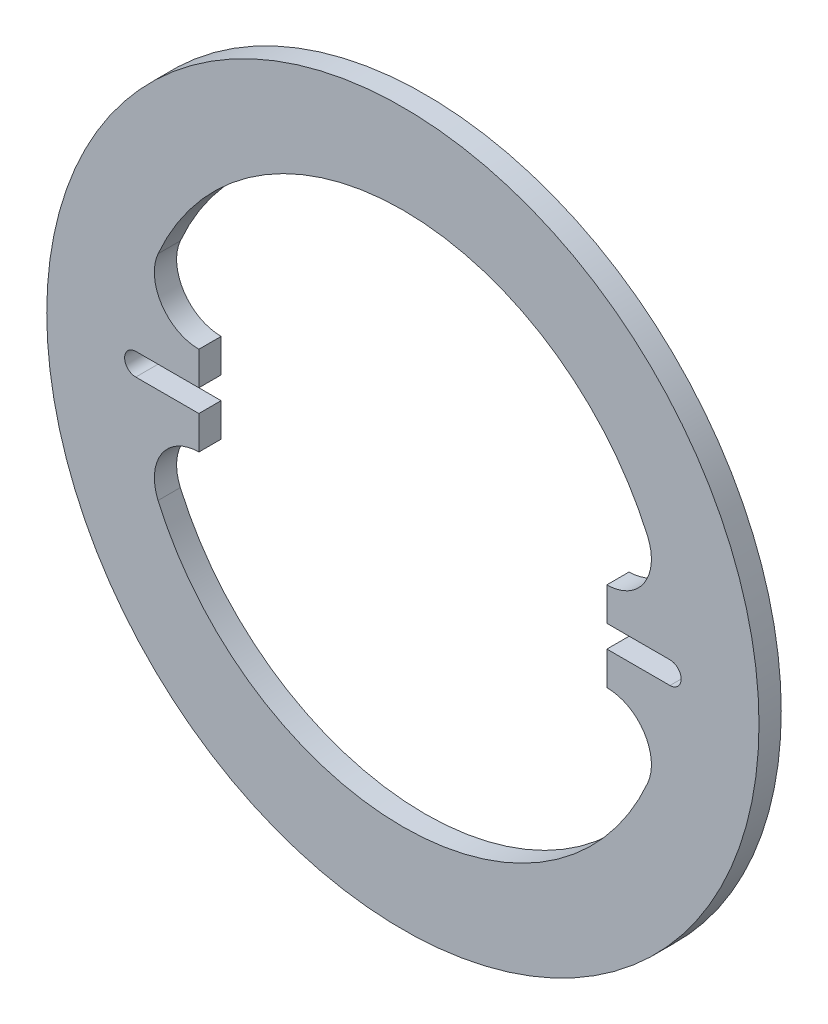
SolidWorks part; units mm, degrees
ref_plane "Front Plane" through (0, 0, 0) normal (0, 0, 1) x (1, 0, 0)
ref_plane "Top Plane" through (0, 0, 0) normal (0, 1, 0) x (1, 0, 0)
ref_plane "Right Plane" through (0, 0, 0) normal (1, 0, 0) x (0, 0, -1)
sketch "Sketch1" plane through (0, 0, 0) normal (0, 0, 1) x (1, 0, 0)
  circle A0 centre (0, 0) radius 101.6
  dimension "D1" = 203.2
extrude "Boss-Extrude1" add sketch "Sketch1" along normal blind 6.35
sketch "Sketch2" plane through (0, 0, 6.35) normal (0, 0, 1) x (1, 0, 0)
  circle A0 centre (0, 0) radius 25.4
  dimension "D1" = 50.8
extrude "Cut-Extrude1" cut sketch "Sketch2" against normal through all
sketch "Sketch3" plane through (0, 0, 6.35) normal (0, 0, 1) x (1, 0, 0)
  line L0 (0, 0) -> (0, 63.5) construction
  line L1 (58.1987, 25.4) -> (-58.1987, 25.4) construction
  circle A0 centre (0, 0) radius 63.5 construction
  arc A1 (-58.1987, 25.4) -> (58.1987, 25.4) centre (0, 0) cw construction
  arc A2 (69.8385, 30.48) -> (-69.8385, 30.48) centre (0, 0) ccw
  arc A3 (46.559, 20.32) -> (-46.559, 20.32) centre (0, 0) ccw
  arc A4 (46.559, 20.32) -> (69.8385, 30.48) centre (58.1987, 25.4) ccw
  arc A5 (-69.8385, 30.48) -> (-46.559, 20.32) centre (-58.1987, 25.4) ccw
  point P5 (0, 63.5)
  dimension "D1" = 127
  dimension "D2" = 25.4
  dimension "D3" = 12.7
extrude "Cut-Extrude2" cut sketch "Sketch3" against normal through all
mirror "Mirror1" about plane through (0, 0, 0) normal (0, 1, 0) of "Cut-Extrude2"
sketch "Sketch4" plane through (0, 0, 6.35) normal (0, 0, 1) x (1, 0, 0)
  line L0 (101.6, 0) -> (-101.6, 0) construction
  line L1 (0, 101.6) -> (0, -101.6) construction
  line L2 (76.2, 0) -> (25.4, 0) construction
  line L3 (-76.2, 0) -> (-25.4, 0) construction
  line L4 (76.2, -3.175) -> (25.4, -3.175)
  line L5 (76.2, 3.175) -> (25.4, 3.175)
  line L6 (-76.2, -3.175) -> (-25.4, -3.175)
  line L7 (-76.2, 3.175) -> (-25.4, 3.175)
  circle A0 centre (0, 0) radius 101.6 construction
  arc A1 (76.2, -3.175) -> (76.2, 3.175) centre (76.2, 0) ccw
  arc A2 (25.4, 3.175) -> (25.4, -3.175) centre (25.4, 0) ccw
  arc A3 (-76.2, -3.175) -> (-76.2, 3.175) centre (-76.2, 0) cw
  arc A4 (-25.4, 3.175) -> (-25.4, -3.175) centre (-25.4, 0) cw
  point P11 (50.8, 0)
  point P16 (-50.8, 0)
  dimension "D1" = 50.8
  dimension "D2" = 50.8
  dimension "D3" = 6.35
extrude "Cut-Extrude3" cut sketch "Sketch4" against normal through all
sketch "Sketch6" [suppressed] plane through (0, 0, 8.89) normal (0, 0, 1) x (1, 0, 0)
  line L0 (-101.6, 0) -> (101.6, 0) construction
  line L1 (-92.202, -3.429) -> (92.202, -3.429)
  line L2 (-92.202, -3.429) -> (-92.202, 3.429)
  line L3 (-92.202, 3.429) -> (92.202, 3.429)
  line L4 (92.202, -3.429) -> (92.202, 3.429)
  line L5 (0, 101.6) -> (0, -101.6) construction
  circle A0 centre (0, 0) radius 101.6 construction
  dimension "D1" = 6.858
  dimension "D2" = 184.404
extrude "Cut-Extrude4" [suppressed] cut sketch "Sketch6" against normal through all
sketch "Sketch7" [suppressed] plane through (0, 0, 8.89) normal (0, 0, 1) x (1, 0, 0)
  line L0 (85.852, -41.2553) -> (85.852, 41.2553)
  line L1 (0, 101.6) -> (0, -101.6) construction
  line L2 (92.202, -3.429) -> (92.202, 3.429) construction
  line L3 (-85.852, -41.2553) -> (-85.852, 41.2553)
  arc A0 (85.852, 41.2553) -> (-85.852, 41.2553) centre (0, 0) ccw
  circle A1 centre (0, 0) radius 101.6 construction
  arc A2 (-85.852, -41.2553) -> (85.852, -41.2553) centre (0, 0) ccw
  dimension "D1" = 6.35
  dimension "D2" = 6.35
extrude "Cut-Extrude5" [suppressed] cut sketch "Sketch7" against normal through all
sketch "Sketch8" [suppressed] plane through (0, 0, 0) normal (0, 0, -1) x (-1, 0, 0)
  line L0 (0, 101.6) -> (0, -101.6) construction
  line L1 (-101.6, 0) -> (101.6, 0) construction
  line L2 (-25.4, 0) -> (25.4, 0) construction
  line L3 (-25.4, 3.302) -> (25.4, 3.302)
  line L4 (-25.4, -3.302) -> (25.4, -3.302)
  line L5 (63.5, 0) -> (88.9, 0) construction
  line L6 (63.5, 3.302) -> (88.9, 3.302)
  line L7 (63.5, -3.302) -> (88.9, -3.302)
  line L8 (-63.5, 0) -> (-88.9, 0) construction
  line L9 (-63.5, 3.302) -> (-88.9, 3.302)
  line L10 (-63.5, -3.302) -> (-88.9, -3.302)
  circle A0 centre (0, 0) radius 101.6 construction
  arc A1 (-25.4, 3.302) -> (-25.4, -3.302) centre (-25.4, 0) ccw
  arc A2 (25.4, -3.302) -> (25.4, 3.302) centre (25.4, 0) ccw
  arc A3 (63.5, 3.302) -> (63.5, -3.302) centre (63.5, 0) ccw
  arc A4 (88.9, -3.302) -> (88.9, 3.302) centre (88.9, 0) ccw
  arc A5 (-63.5, 3.302) -> (-63.5, -3.302) centre (-63.5, 0) cw
  arc A6 (-88.9, -3.302) -> (-88.9, 3.302) centre (-88.9, 0) cw
  point P9 (0, 0)
  point P17 (76.2, 0)
  point P24 (-76.2, 0)
  dimension "D1" = 50.8
  dimension "D2" = 6.604
  dimension "D3" = 25.4
  dimension "D4" = 25.4
extrude "Cut-Extrude6" [suppressed] cut sketch "Sketch8" against normal through all
sketch "Sketch9" [suppressed] plane through (0, 0, 6.35) normal (0, 0, 1) x (1, 0, 0)
  line L0 (-101.6, 0) -> (101.6, 0) construction
  line L1 (0, 101.6) -> (0, -101.6) construction
  circle A0 centre (0, 0) radius 101.6 construction
  circle A1 centre (47.498, 0) radius 2.54
  circle A2 centre (-47.498, 0) radius 2.54
  dimension "D1" = 5.08
  dimension "D2" = 94.996
extrude "Cut-Extrude7" [suppressed] cut sketch "Sketch9" against normal through all
sketch "Sketch10" [suppressed] plane through (0, 0, 6.35) normal (0, 0, 1) x (1, 0, 0)
  line L5 (-14.986, -19.558) -> (14.986, -19.558)
  line L6 (-14.986, -19.558) -> (-14.986, -14.478)
  line L7 (-14.986, -14.478) -> (14.986, -14.478)
  line L8 (14.986, -19.558) -> (14.986, -14.478)
  point P4 (0, -14.478)
  dimension "D1" = 5.08
  dimension "D2" = 29.972
  dimension "D3" = 14.478
extrude "Boss-Extrude2" [suppressed] add sketch "Sketch10" along normal blind 25.908
sketch "Sketch11" [suppressed] plane through (14.986, 0, 0) normal (1, 0, 0) x (0, 0, -1)
  line L0 (-32.258, -19.558) -> (-6.35, -34.516)
  line L1 (-6.35, 101.6) -> (-6.35, -101.6) construction
  line L2 (-6.35, -34.516) -> (-6.35, -19.558)
  line L3 (-6.35, -19.558) -> (-32.258, -19.558)
  dimension "D1" = 30
extrude "Boss-Extrude3" [suppressed] add sketch "Sketch11" against normal blind 5.08
ref_plane "Plane1" [suppressed] through (0, 0, 0) normal (1, 0, 0) x (0, 0, -1)
mirror "Mirror2" [suppressed] about plane through (0, 0, 0) normal (1, 0, 0)
sketch "Sketch12" [suppressed] plane through (0, -14.478, 0) normal (0, 1, 0) x (1, 0, 0)
  line L0 (14.986, -32.258) -> (-14.986, -32.258) construction
  circle A0 centre (0, -16.51) radius 3.937
  dimension "D1" = 7.874
  dimension "D2" = 15.748
extrude "Cut-Extrude8" [suppressed] cut sketch "Sketch12" against normal through all
sketch "Sketch13" [suppressed] plane through (0, 0, 6.35) normal (0, 0, 1) x (1, 0, 0)
  line L0 (-100.8031, 12.7) -> (100.8031, 12.7) construction
  line L1 (-91.836, 12.7) -> (91.836, 12.7)
  circle A0 centre (0, 0) radius 101.6 construction
  arc A1 (-69.8385, 30.48) -> (-46.559, 20.32) centre (-58.1987, 25.4) ccw construction
  arc A2 (-91.836, 12.7) -> (91.836, 12.7) centre (0, 0) cw
  dimension "D1" = 8.89
extrude "Cut-Extrude9" [suppressed] cut sketch "Sketch13" against normal through all
sketch "Sketch14" plane through (0, 0, 6.35) normal (0, 0, 1) x (1, 0, 0)
  line L0 (-58.1987, -12.7) -> (-58.1987, 12.7)
  line L1 (58.1987, 12.7) -> (58.1987, -12.7)
  arc A0 (-46.559, -20.32) -> (-69.8385, -30.48) centre (-58.1987, -25.4) ccw construction
  arc A1 (-69.8385, 30.48) -> (-46.559, 20.32) centre (-58.1987, 25.4) ccw construction
  arc A2 (46.559, 20.32) -> (69.8385, 30.48) centre (58.1987, 25.4) ccw construction
  arc A3 (69.8385, -30.48) -> (46.559, -20.32) centre (58.1987, -25.4) ccw construction
  arc A4 (46.559, 20.32) -> (-46.559, 20.32) centre (0, 0) ccw construction
  arc A5 (-46.559, -20.32) -> (46.559, -20.32) centre (0, 0) ccw construction
  arc A6 (46.559, 20.32) -> (58.1987, 12.7) centre (58.1987, 25.4) ccw
  arc A7 (58.1987, -12.7) -> (46.559, -20.32) centre (58.1987, -25.4) ccw
  arc A8 (-46.559, -20.32) -> (-58.1987, -12.7) centre (-58.1987, -25.4) ccw
  arc A9 (-58.1987, 12.7) -> (-46.559, 20.32) centre (-58.1987, 25.4) ccw
  arc A10 (46.559, 20.32) -> (-46.559, 20.32) centre (0, 0) ccw
  arc A11 (-46.559, -20.32) -> (46.559, -20.32) centre (0, 0) ccw
extrude "Cut-Extrude10" cut sketch "Sketch14" against normal through all
